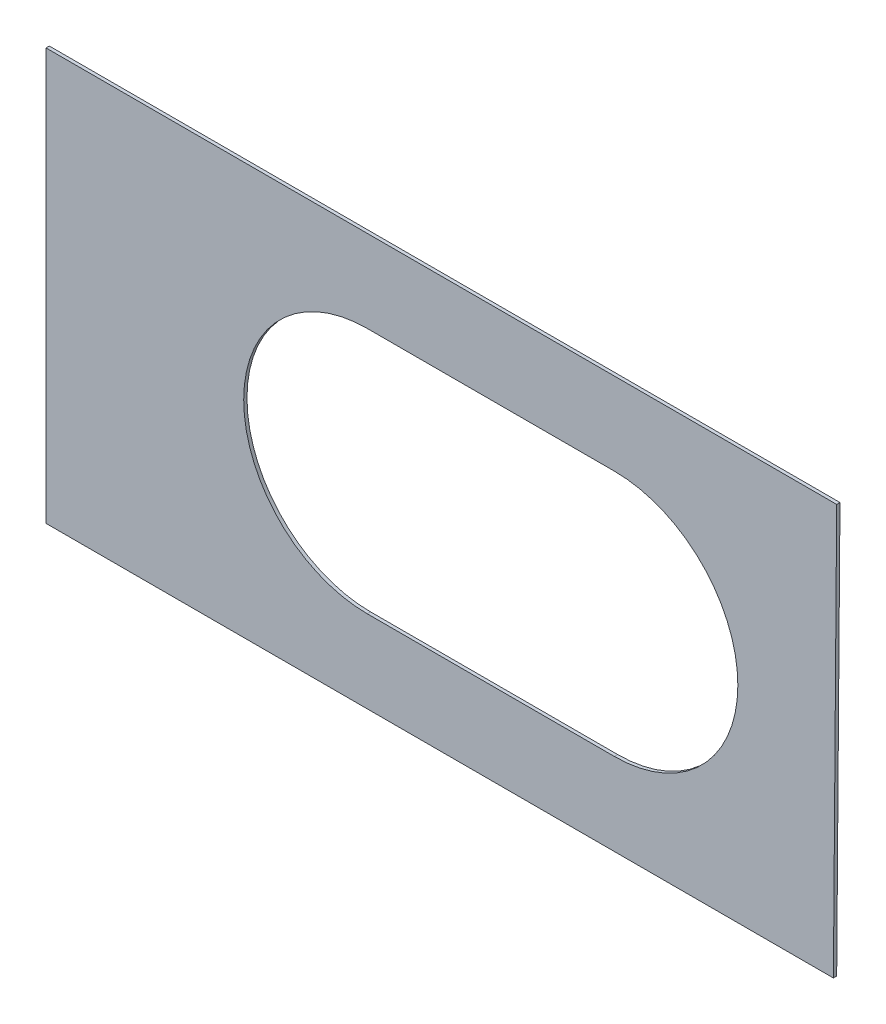
SolidWorks part; units mm, degrees
ref_plane "Front Plane" through (0, 0, 0) normal (0, 0, 1) x (1, 0, 0)
ref_plane "Top Plane" through (0, 0, 0) normal (0, 1, 0) x (1, 0, 0)
ref_plane "Right Plane" through (0, 0, 0) normal (1, 0, 0) x (0, 0, -1)
sketch "Model" plane through (0, 0, 0) normal (0, 0, 1) x (1, 0, 0)
  line L0 (-45, 0) -> (105, 0) construction
  line L1 (-240, 125) -> (240, 125)
  line L2 (-240, 125) -> (-240, -125)
  line L3 (-240, -125) -> (238, -125)
  line L4 (240, 125) -> (238, -125)
  line L5 (-240, 125) -> (238, -125) construction
  line L6 (-240, -125) -> (240, 125) construction
  line L7 (-45, 75) -> (105, 75)
  line L8 (-45, -75) -> (105, -75)
  line L9 (238, -125) -> (-242, -125) construction
  arc A0 (-45, 75) -> (-45, -75) centre (-45, 0) ccw
  arc A1 (105, -75) -> (105, 75) centre (105, 0) ccw
  point P10 (0, 0)
  point P11 (30, 0)
  point P12 (0, 0)
  point P13 (238, -125)
extrude "Boss-Extrude1" add sketch "Model" along normal blind 2
